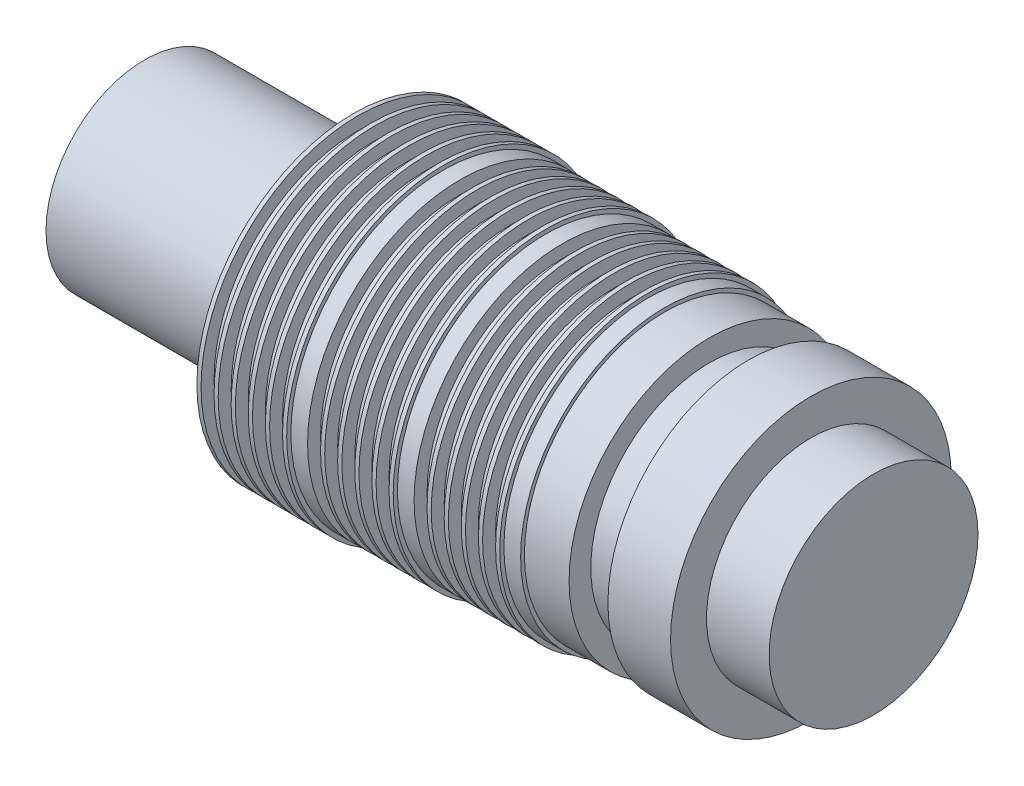
SolidWorks part; units mm, degrees
ref_plane "Front Plane" through (0, 0, 0) normal (0, 0, 1) x (1, 0, 0)
ref_plane "Top Plane" through (0, 0, 0) normal (0, 1, 0) x (1, 0, 0)
ref_plane "Right Plane" through (0, 0, 0) normal (1, 0, 0) x (0, 0, -1)
sketch "Sketch1" plane through (0, 0, 0) normal (0, 0, 1) x (1, 0, 0)
  line L24 (12.954, 9.525) -> (12.954, 8.7376)
  line L25 (12.954, 8.7376) -> (13.7414, 8.7376)
  line L26 (13.7414, 8.7376) -> (13.7414, 9.525)
  line L27 (13.7414, 9.525) -> (13.9954, 9.525)
  line L28 (13.9954, 9.525) -> (13.9954, 8.7376)
  line L29 (13.9954, 8.7376) -> (14.7828, 8.7376)
  line L30 (14.7828, 8.7376) -> (14.7828, 9.525)
  line L31 (14.7828, 9.525) -> (15.0368, 9.525)
  line L32 (15.0368, 9.525) -> (15.0368, 8.7376)
  line L33 (15.0368, 8.7376) -> (15.8242, 8.7376)
  line L34 (15.8242, 8.7376) -> (15.8242, 9.525)
  line L35 (15.8242, 9.525) -> (16.0782, 9.525)
  line L36 (16.0782, 9.525) -> (16.0782, 8.7376)
  line L37 (16.0782, 8.7376) -> (16.8656, 8.7376)
  line L38 (16.8656, 8.7376) -> (16.8656, 9.525)
  line L39 (16.8656, 9.525) -> (17.1196, 9.525)
  line L40 (17.1196, 9.525) -> (17.1196, 8.7376)
  line L41 (17.1196, 8.7376) -> (17.907, 8.7376)
  line L42 (17.907, 8.7376) -> (17.907, 9.525)
  line L43 (17.907, 9.525) -> (18.161, 9.525)
  line L44 (18.161, 9.525) -> (18.161, 9.271)
  line L45 (18.161, 9.271) -> (19.177, 9.271)
  line L46 (19.177, 9.271) -> (19.177, 8.4836)
  line L47 (19.177, 8.4836) -> (19.9644, 8.4836)
  line L48 (19.9644, 8.4836) -> (19.9644, 9.271)
  line L49 (19.9644, 9.271) -> (20.2184, 9.271)
  line L50 (20.2184, 9.271) -> (20.2184, 8.4836)
  line L51 (20.2184, 8.4836) -> (21.0058, 8.4836)
  line L52 (21.0058, 8.4836) -> (21.0058, 9.271)
  line L53 (21.0058, 9.271) -> (21.2598, 9.271)
  line L54 (21.2598, 9.271) -> (21.2598, 8.4836)
  line L55 (21.2598, 8.4836) -> (22.0472, 8.4836)
  line L56 (22.0472, 8.4836) -> (22.0472, 9.271)
  line L57 (22.0472, 9.271) -> (22.3012, 9.271)
  line L58 (22.3012, 9.271) -> (22.3012, 8.4836)
  line L59 (22.3012, 8.4836) -> (23.0886, 8.4836)
  line L60 (23.0886, 8.4836) -> (23.0886, 9.271)
  line L61 (23.0886, 9.271) -> (23.3426, 9.271)
  line L62 (23.3426, 9.271) -> (23.3426, 8.4836)
  line L63 (23.3426, 8.4836) -> (24.13, 8.4836)
  line L64 (24.13, 8.4836) -> (24.13, 9.271)
  line L65 (24.13, 9.271) -> (24.384, 9.271)
  line L66 (24.384, 9.271) -> (24.384, 9.017)
  line L67 (24.384, 9.017) -> (25.4, 9.017)
  line L68 (25.4, 9.017) -> (25.4, 8.2296)
  line L69 (25.4, 8.2296) -> (26.1874, 8.2296)
  line L70 (26.1874, 8.2296) -> (26.1874, 9.017)
  line L71 (26.1874, 9.017) -> (26.4414, 9.017)
  line L72 (26.4414, 9.017) -> (26.4414, 8.2296)
  line L73 (26.4414, 8.2296) -> (27.2288, 8.2296)
  line L74 (27.2288, 8.2296) -> (27.2288, 9.017)
  line L75 (27.2288, 9.017) -> (27.4828, 9.017)
  line L76 (27.4828, 9.017) -> (27.4828, 8.2296)
  line L77 (27.4828, 8.2296) -> (28.2702, 8.2296)
  line L78 (28.2702, 8.2296) -> (28.2702, 9.017)
  line L79 (28.2702, 9.017) -> (28.5242, 9.017)
  line L80 (28.5242, 9.017) -> (28.5242, 8.2296)
  line L81 (28.5242, 8.2296) -> (29.3116, 8.2296)
  line L82 (29.3116, 8.2296) -> (29.3116, 9.017)
  line L83 (29.3116, 9.017) -> (29.5656, 9.017)
  line L84 (29.5656, 9.017) -> (29.5656, 8.2296)
  line L85 (29.5656, 8.2296) -> (30.353, 8.2296)
  line L86 (30.353, 8.2296) -> (30.353, 9.017)
  line L87 (30.353, 9.017) -> (30.607, 9.017)
  line L88 (30.607, 9.017) -> (30.607, 8.763)
  line L89 (30.607, 8.763) -> (31.623, 8.763)
  line L90 (31.623, 8.763) -> (31.623, 7.9756)
  line L91 (31.623, 7.9756) -> (32.4104, 7.9756)
  line L92 (32.4104, 7.9756) -> (32.4104, 8.763)
  line L93 (32.4104, 8.763) -> (32.6644, 8.763)
  line L94 (32.6644, 8.763) -> (32.6644, 7.9756)
  line L95 (32.6644, 7.9756) -> (33.4518, 7.9756)
  line L96 (33.4518, 7.9756) -> (33.4518, 8.763)
  line L97 (33.4518, 8.763) -> (33.7058, 8.763)
  line L98 (33.7058, 8.763) -> (33.7058, 7.9756)
  line L99 (33.7058, 7.9756) -> (34.4932, 7.9756)
  line L100 (34.4932, 7.9756) -> (34.4932, 8.763)
  line L101 (34.4932, 8.763) -> (34.7472, 8.763)
  line L102 (34.7472, 8.763) -> (34.7472, 7.9756)
  line L103 (34.7472, 7.9756) -> (35.5346, 7.9756)
  line L104 (35.5346, 7.9756) -> (35.5346, 8.763)
  line L105 (35.5346, 8.763) -> (35.7886, 8.763)
  line L106 (35.7886, 8.763) -> (35.7886, 7.9756)
  line L107 (35.7886, 7.9756) -> (36.576, 7.9756)
  line L108 (36.576, 7.9756) -> (36.576, 8.763)
  line L109 (36.576, 8.763) -> (36.83, 8.763)
  line L110 (36.83, 8.763) -> (36.83, 8.509)
  line L111 (36.83, 8.509) -> (37.846, 8.509)
  line L112 (37.846, 8.509) -> (37.846, 7.7216)
  line L113 (37.846, 7.7216) -> (38.6334, 7.7216)
  line L114 (38.6334, 7.7216) -> (38.6334, 8.509)
  line L115 (38.6334, 8.509) -> (38.8874, 8.509)
  line L116 (38.8874, 8.509) -> (38.8874, 7.7216)
  line L117 (38.8874, 7.7216) -> (39.6748, 7.7216)
  line L118 (39.6748, 7.7216) -> (39.6748, 8.509)
  line L119 (39.6748, 8.509) -> (39.9288, 8.509)
  line L120 (39.9288, 8.509) -> (39.9288, 7.7216)
  line L121 (39.9288, 7.7216) -> (40.7162, 7.7216)
  line L122 (40.7162, 7.7216) -> (40.7162, 8.509)
  line L123 (40.7162, 8.509) -> (40.9702, 8.509)
  line L124 (40.9702, 8.509) -> (40.9702, 7.7216)
  line L125 (40.9702, 7.7216) -> (41.7576, 7.7216)
  line L126 (41.7576, 7.7216) -> (41.7576, 8.509)
  line L127 (41.7576, 8.509) -> (42.0116, 8.509)
  line L128 (42.0116, 8.509) -> (42.0116, 7.7216)
  line L129 (42.0116, 7.7216) -> (42.799, 7.7216)
  line L130 (42.799, 7.7216) -> (42.799, 8.509)
  line L131 (42.799, 8.509) -> (43.053, 8.509)
  line L132 (43.053, 8.509) -> (43.053, 8.255)
  line L133 (43.053, 8.255) -> (44.069, 8.255)
  line L134 (44.069, 8.255) -> (44.069, 7.4676)
  line L135 (44.069, 7.4676) -> (44.8564, 7.4676)
  line L136 (44.8564, 7.4676) -> (44.8564, 8.255)
  line L137 (44.8564, 8.255) -> (45.1104, 8.255)
  line L138 (45.1104, 8.255) -> (45.1104, 7.4676)
  line L139 (45.1104, 7.4676) -> (45.8978, 7.4676)
  line L140 (45.8978, 7.4676) -> (45.8978, 8.255)
  line L141 (45.8978, 8.255) -> (46.1518, 8.255)
  line L142 (46.1518, 8.255) -> (46.1518, 7.4676)
  line L143 (46.1518, 7.4676) -> (46.9392, 7.4676)
  line L144 (46.9392, 7.4676) -> (46.9392, 8.255)
  line L145 (46.9392, 8.255) -> (47.1932, 8.255)
  line L146 (47.1932, 8.255) -> (47.1932, 7.4676)
  line L147 (47.1932, 7.4676) -> (47.9806, 7.4676)
  line L148 (47.9806, 7.4676) -> (47.9806, 8.255)
  line L149 (47.9806, 8.255) -> (48.2346, 8.255)
  line L150 (48.2346, 8.255) -> (48.2346, 7.4676)
  line L151 (48.2346, 7.4676) -> (49.022, 7.4676)
  line L152 (49.022, 7.4676) -> (49.022, 8.255)
  line L153 (49.022, 8.255) -> (49.276, 8.255)
  line L156 (12.7, 6) -> (0, 6)
  line L157 (0, 6) -> (0, 0)
  line L158 (0, 0) -> (61.976, 0)
  line L160 (12.954, 9.525) -> (12.7, 9.525)
  line L161 (12.7, 9.525) -> (12.7, 6)
  line L162 (49.276, 6) -> (74.676, 6)
  line L163 (74.676, 6) -> (74.676, 0)
  line L164 (74.676, 0) -> (61.976, 0)
  line L165 (49.276, 8.255) -> (49.276, 6)
  point P5 (12.827, 9.525)
  point P6 (61.976, 6)
  dimension "D1" = 6
  dimension "D9" = 12.7
  dimension "D3" = 0.254
  dimension "D4" = 0.7874
  dimension "D5" = 0.7874
  dimension "D7" = 1.016
  dimension "D10" = 6
  dimension "D11" = 25.4
  dimension "D2" = 9.525
  dimension "D6" = 0.254
revolve "Revolve1" add sketch "Sketch1" angle 360 about L158
ref_plane "split plane" through (31.623, 0, 0) normal (1, 0, 0) x (0, 0, -1)
sketch "Sketch3" plane through (31.623, 0, 0) normal (1, 0, 0) x (0, 0, -1)
  circle A0 centre (0, 0) radius 17.3578
extrude "Cut-Extrude1" cut sketch "Sketch3" along normal blind 114.5794
sketch "Sketch4" plane through (31.623, 0, 0) normal (1, 0, 0) x (0, 0, -1)
  circle A0 centre (0, 0) radius 6.35
  dimension "D1" = 12.7
extrude "Boss-Extrude1" add sketch "Sketch4" along normal blind 12.7
sketch "Sketch5" plane through (31.623, 0, 0) normal (1, 0, 0) x (0, 0, -1)
  circle A0 centre (0, 0) radius 8.5344
  circle A1 centre (0, 0) radius 6.35 construction
  circle A2 centre (0, 0) radius 6.35
  dimension "D1" = 17.0688
extrude "Boss-Extrude2" add sketch "Sketch5" along normal blind 8.89
sketch "Sketch6" plane through (40.513, 0, 0) normal (1, 0, 0) x (0, 0, -1)
  circle A0 centre (0, 0) radius 7.2136
  circle A1 centre (0, 0) radius 8.5344 construction
  circle A2 centre (0, 0) radius 8.5344
  dimension "D1" = 14.4272
extrude "Cut-Extrude2" cut sketch "Sketch6" against normal blind 2.3622 from offset 3.81
equation "\"kero_radius\"=0.23622in"
equation "\"D1@Sketch1\"=\"kero_radius\""
equation "\"lox_radius\"=0.23622in"
equation "\"Cavity_width\"=0.031in"
equation "\"tooth_width\"=0.01in"
equation "\"cavity_depth\"=0.031in"
equation "\"seal_step\"=0.01in"
equation "\"purge_length\"=0.04in"
equation "\"D3@Sketch1\"=\"tooth_width\""
equation "\"D4@Sketch1\"=\"Cavity_width\""
equation "\"D5@Sketch1\"=\"cavity_depth\""
equation "\"D7@Sketch1\"=\"purge_length\""
equation "\"D10@Sketch1\"=\"lox_radius\""
equation "\"lox_in_radius\"=.375in"
equation "\"bearing_radius\"= 0.629921"
equation "\"bearing_width\"=0.393701"
equation "\"insert_radius\" = 0.5925in"
equation "\"recycle_groove width\" = 0.05in"
equation "\"recycle_groove_depth\" = 0.04in"
equation "\"N2_purge_width\"= .05in"
equation "\"N2_purge_depth\"= .04in"
equation "\"drain_width\"= .05in"
equation "\"drain_depth\"= .04in"
equation "\"radial_clearance\"= .002in"
equation "\"IPS_flange_width\"= .25in"
equation "\"IPS_flange_radius\" = 2.2in"
equation "\"IPS_LOX_male_radius\"= .9in"
equation "\"IPS_Kero_male_radius\" = .9in"
equation "\"IPS_radius\"= 1.4in"
equation "\"InsertLength\"= 1.445in"
equation "\"D2@Sketch1\"=\"lox_in_radius\""
equation "\"D6@Sketch1\"=\"seal_step\""
